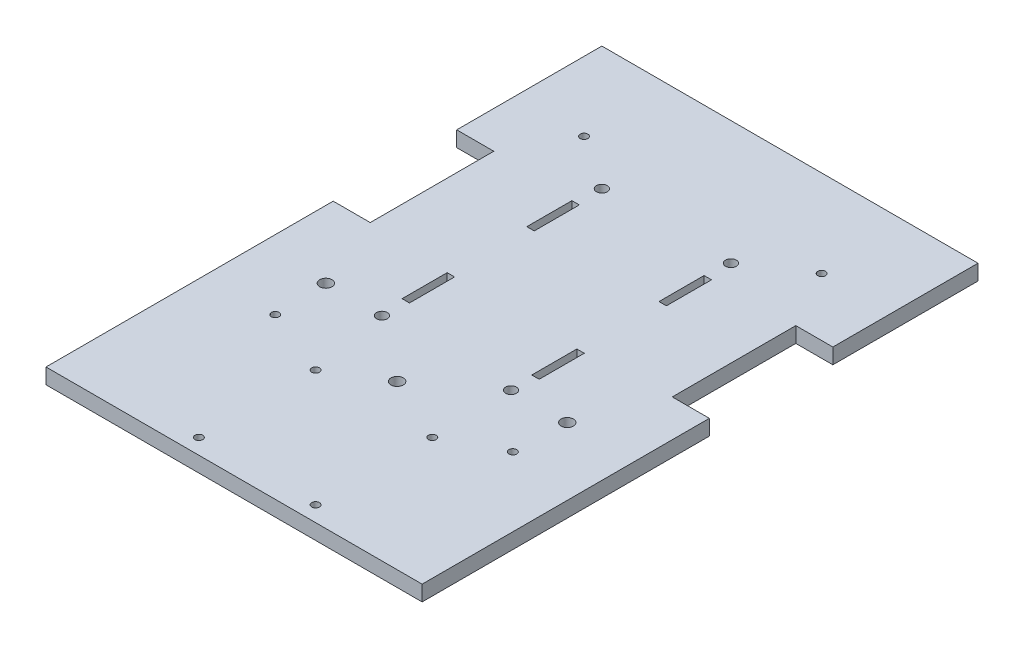
SolidWorks part; units mm, degrees
ref_plane "Front Plane" through (0, 0, 0) normal (0, 0, 1) x (1, 0, 0)
ref_plane "Top Plane" through (0, 0, 0) normal (0, 1, 0) x (1, 0, 0)
ref_plane "Right Plane" through (0, 0, 0) normal (1, 0, 0) x (0, 0, -1)
sketch "Sketch1" plane through (0, 0, 0) normal (0, 1, 0) x (1, 0, 0)
  circle A0 centre (0, 90.4441) radius 2.2225
  circle A1 centre (53.086, 90.4441) radius 2.2225
  circle A2 centre (0, 0) radius 2.2225
  circle A3 centre (53.086, 0) radius 2.2225
  dimension "D1" = 4.445
  dimension "D2" = 4.445
  dimension "D3" = 4.445
  dimension "D4" = 4.445
  dimension "D5" = 53.086
  dimension "D6" = 90.4441
  dimension "D7" = 104.8725
  dimension "D8" = 0
  dimension "D10" = 104.8725
  dimension "D11" = 53.086
  dimension "D9" = 53.086
sketch "Sketch2" plane through (0, 0, 0) normal (0, 1, 0) x (1, 0, 0)
  line L1 (-50.8, 141.2441) -> (103.886, 141.2441)
  line L2 (-50.8, 141.2441) -> (-50.8, -87.3559)
  line L3 (-50.8, -87.3559) -> (103.886, -87.3559)
  line L4 (103.886, 141.2441) -> (103.886, -87.3559)
  circle A0 centre (0, 90.4441) radius 2.2225 construction
  circle A1 centre (53.086, 90.4441) radius 2.2225 construction
  dimension "D3" = 50.8
  dimension "D1" = 50.8
  dimension "D2" = 50.8
  dimension "D4" = 228.6
extrude "Boss-Extrude1" add sketch "Sketch2" along normal blind 6.35
extrude "Cut-Extrude1" cut sketch "Sketch1" along normal blind 6.35
sketch "Sketch3" plane through (0, 6.35, 0) normal (0, 1, 0) x (1, 0, 0)
  line L0 (103.886, -87.3559) -> (103.886, 141.2441) construction
  line L1 (103.886, 81.5541) -> (88.646, 81.5541)
  line L2 (103.886, 81.5541) -> (103.886, 30.7541)
  line L3 (103.886, 30.7541) -> (88.646, 30.7541)
  line L4 (88.646, 81.5541) -> (88.646, 30.7541)
  line L5 (-50.8, 141.2441) -> (-50.8, -87.3559) construction
  line L6 (-50.8, 81.5541) -> (-35.56, 81.5541)
  line L7 (-50.8, 81.5541) -> (-50.8, 30.7541)
  line L8 (-50.8, 30.7541) -> (-35.56, 30.7541)
  line L9 (-35.56, 81.5541) -> (-35.56, 30.7541)
  circle A0 centre (0, 90.4441) radius 2.2225 construction
  point P12 (96.266, 81.5541)
  dimension "D1" = 15.24
  dimension "D2" = 15.24
  dimension "D3" = 0
  dimension "D4" = 50.8
  dimension "D5" = 50.8
  dimension "D6" = 8.89
extrude "Cut-Extrude2" cut sketch "Sketch3" against normal blind 6.35
sketch "Sketch8" plane through (0, 6.35, 0) normal (0, 1, 0) x (1, 0, 0)
  circle A0 centre (26.5501, -20.2997) radius 2.54
  circle A1 centre (-23.0771, 0.0203) radius 2.54
  circle A2 centre (76.1773, 0.0203) radius 2.54
  dimension "D1" = 5.08
  dimension "D2" = 5.08
  dimension "D3" = 5.08
  dimension "D4" = 49.6272
  dimension "D5" = 20.32
  dimension "D6" = 49.6272
  dimension "D7" = 20.32
  dimension "D9" = 26.5501
  dimension "D8" = 20.2997
extrude "Cut-Extrude3" cut sketch "Sketch8" against normal blind 17.78
sketch "Sketch9" plane through (0, 6.35, 0) normal (0, 1, 0) x (1, 0, 0)
  line L0 (29.7251, -13.9559) -> (29.7251, -121.9059)
  line L1 (-50.8, -87.3559) -> (103.886, -87.3559) construction
  circle A0 centre (53.7221, -33.0059) radius 1.5875
  circle A1 centre (53.7221, -81.0059) radius 1.5875
  circle A2 centre (5.7221, -81.0059) radius 1.5875
  circle A3 centre (5.7221, -33.0059) radius 1.5875
  circle A5 centre (26.5501, -20.2997) radius 2.54 construction
  dimension "D1" = 48
  dimension "D2" = 48
  dimension "D3" = 48
  dimension "D4" = 48
  dimension "D5" = 3.175
  dimension "D6" = 3.175
  dimension "D7" = 3.175
  dimension "D8" = 3.175
  dimension "D9" = 24.003
  dimension "D10" = 6.35
  dimension "D11" = 0
  dimension "D12" = 0
  dimension "D14" = 107.95
  dimension "D13" = 3.175
  dimension "D15" = 13.9559
extrude "Cut-Extrude4" cut sketch "Sketch9" against normal blind 17.78 contours A0 | A3 | A1 | A2
sketch "Sketch10" plane through (0, 6.35, 0) normal (0, 1, 0) x (1, 0, 0)
  circle A0 centre (-22.3266, 105.4301) radius 1.5875
  circle A1 centre (0, 90.4441) radius 2.2225 construction
  circle A2 centre (-22.3266, -21.5699) radius 1.5875
  circle A3 centre (75.4126, 105.4301) radius 1.5875
  circle A4 centre (53.086, 90.4441) radius 2.2225 construction
  circle A5 centre (75.4126, -21.5699) radius 1.5875
  point P12 (88.4771, -21.5699)
  dimension "D1" = 3.175
  dimension "D2" = 22.3266
  dimension "D3" = 14.986
  dimension "D4" = 3.175
  dimension "D5" = 127
  dimension "D6" = 0
  dimension "D7" = 3.175
  dimension "D8" = 14.986
  dimension "D9" = 22.3266
  dimension "D10" = 3.175
  dimension "D11" = 127
  dimension "D12" = 0
extrude "Cut-Extrude5" cut sketch "Sketch10" against normal blind 10.16
sketch "Sketch12" plane through (0, 6.35, 0) normal (0, 1, 0) x (1, 0, 0)
  line L1 (-1.8979, 10.1801) -> (1.1501, 10.1801)
  line L2 (-1.8979, 10.1801) -> (-1.8979, 28.7221)
  line L3 (-1.8979, 28.7221) -> (1.1501, 28.7221)
  line L4 (1.1501, 10.1801) -> (1.1501, 28.7221)
  line L5 (-1.8979, 61.4881) -> (1.1501, 61.4881)
  line L6 (-1.8979, 61.4881) -> (-1.8979, 80.0301)
  line L7 (-1.8979, 80.0301) -> (1.1501, 80.0301)
  line L8 (1.1501, 61.4881) -> (1.1501, 80.0301)
  line L9 (51.9501, 80.5381) -> (54.9981, 80.5381)
  line L10 (51.9501, 80.5381) -> (51.9501, 61.9961)
  line L11 (51.9501, 61.9961) -> (54.9981, 61.9961)
  line L12 (54.9981, 80.5381) -> (54.9981, 61.9961)
  line L13 (51.9501, 28.2141) -> (54.9981, 28.2141)
  line L14 (51.9501, 28.2141) -> (51.9501, 9.6721)
  line L15 (51.9501, 9.6721) -> (54.9981, 9.6721)
  line L16 (54.9981, 28.2141) -> (54.9981, 9.6721)
  circle A0 centre (26.5501, -20.2997) radius 2.54 construction
  circle A1 centre (-22.3266, 105.4301) radius 1.5875 construction
  circle A2 centre (-22.3266, -21.5699) radius 1.5875 construction
  dimension "D1" = 3.048
  dimension "D2" = 3.048
  dimension "D3" = 18.542
  dimension "D4" = 18.542
  dimension "D5" = 25.4
  dimension "D6" = 0
  dimension "D7" = 25.4
  dimension "D8" = 31.75
  dimension "D9" = 18.542
  dimension "D10" = 18.542
  dimension "D11" = 3.048
  dimension "D12" = 3.048
  dimension "D13" = 50.8
  dimension "D14" = 50.8
  dimension "D15" = 19.05
  dimension "D16" = 19.05
extrude "Cut-Extrude7" cut sketch "Sketch12" against normal blind 8.255
